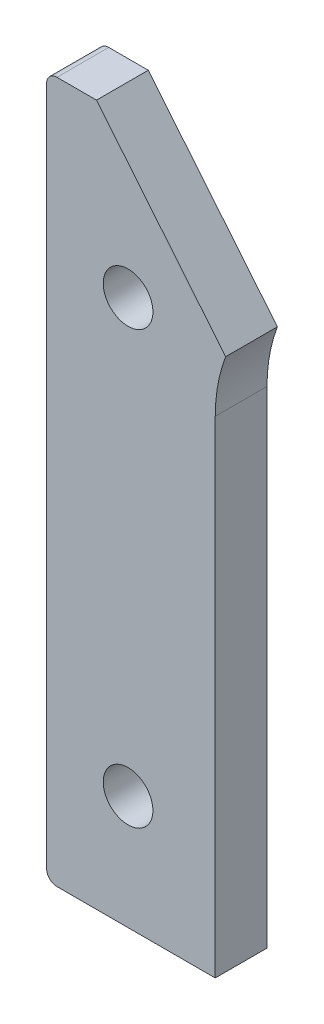
SolidWorks part; units mm, degrees
material "ASTM A36 Steel"
ref_plane "Front Plane" through (0, 0, 0) normal (0, 0, 1) x (1, 0, 0)
ref_plane "Top Plane" through (0, 0, 0) normal (0, 1, 0) x (1, 0, 0)
ref_plane "Right Plane" through (0, 0, 0) normal (1, 0, 0) x (0, 0, -1)
sketch "Sketch1" plane through (0, 0, 0) normal (0, 0, 1) x (1, 0, 0)
  line L1 (5.5978, 13.2827) -> (5.5978, 26.3124)
  line L2 (5.5978, 26.3124) -> (20.32, 26.3124)
  line L3 (21.59, 25.0424) -> (21.59, 0)
  line L4 (0, -21.59) -> (-39.1074, -21.59)
  line L6 (-40.3774, -20.32) -> (-40.3774, 25.0424)
  line L7 (-39.1074, 26.3124) -> (-34.2539, 26.3124)
  line L8 (-34.2539, 26.3124) -> (-14.5989, 2.3182)
  line L9 (-19.685, 0) -> (-19.685, -21.59)
  line L10 (-40.3774, -20.32) -> (-40.3774, -58.42)
  line L11 (-39.1074, -59.69) -> (-19.685, -59.69)
  line L12 (-19.685, -59.69) -> (-19.685, -21.59)
  circle A0 centre (0, 0) radius 19.05 construction
  circle A1 centre (0, 0) radius 6.985
  arc A2 (-12.3786, 2.839) -> (3.9343, 12.0752) centre (0, 0) cw
  arc A5 (21.59, 0) -> (0, -21.59) centre (0, 0) cw
  arc A6 (-12.3786, 2.839) -> (-14.5989, 2.3182) centre (-13.6165, 3.1229) cw
  arc A7 (3.9343, 12.0752) -> (5.5978, 13.2827) centre (4.3278, 13.2827) ccw
  arc A8 (20.32, 26.3124) -> (21.59, 25.0424) centre (20.32, 25.0424) cw
  arc A9 (-40.3774, 25.0424) -> (-39.1074, 26.3124) centre (-39.1074, 25.0424) cw
  arc A10 (-39.1074, -21.59) -> (-40.3774, -20.32) centre (-39.1074, -20.32) cw
  arc A11 (-18.4097, 6.9702) -> (-19.685, 0) centre (0, 0) ccw
  arc A12 (-40.3774, -58.42) -> (-39.1074, -59.69) centre (-39.1074, -58.42) ccw
  circle A13 centre (-30.3825, -45.72) radius 3.048
  circle A14 centre (-30.3825, 7.2624) radius 3.048
  point P22 (-12.7, 0)
  point P31 (-40.3774, -59.69)
  dimension "D1" = 38.1
  dimension "D2" = 13.97
  dimension "D3" = 21.59
  dimension "D4" = 12.7
  dimension "D5" = 1.27
  dimension "D6" = 1.27
  dimension "D7" = 1.27
  dimension "D8" = 19.685
  dimension "D10" = 1.27
  dimension "D11" = 6.096
  dimension "D14" = 6.096
  dimension "D9" = 39.37
  dimension "D12" = 9.9949
  dimension "D13" = 13.97
  dimension "D15" = 19.05
  dimension "D16" = 9.9949
extrude "Boss-Extrude2" add sketch "Sketch1" along normal blind 6.35 contours A11 L8 L7 A9 L6 A10 L4 L9 | L10 A12 L11 L12 L4 A10
